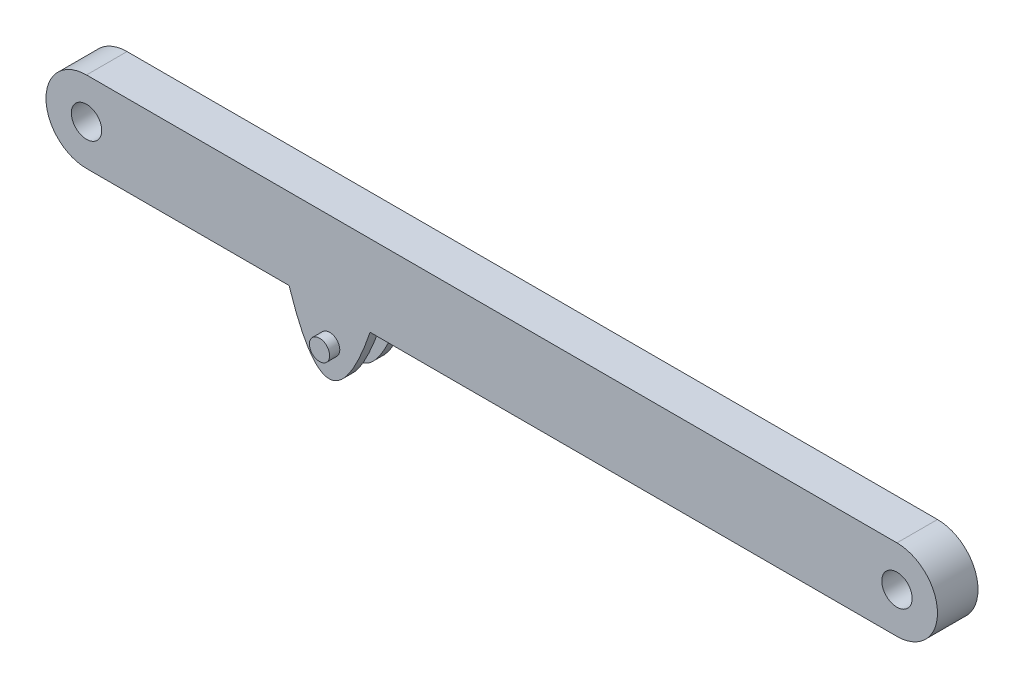
SolidWorks part; units mm, degrees
material "AISI 304"
ref_plane "Front Plane" through (0, 0, 0) normal (0, 0, 1) x (1, 0, 0)
ref_plane "Top Plane" through (0, 0, 0) normal (0, 1, 0) x (1, 0, 0)
ref_plane "Right Plane" through (0, 0, 0) normal (1, 0, 0) x (0, 0, -1)
sketch "Sketch2" plane through (0, 0, 0) normal (0, 0, 1) x (1, 0, 0)
  line L0 (-200, 0) -> (200, 0) construction
  line L1 (-200, 20) -> (200, 20)
  line L2 (-200, -20) -> (200, -20)
  arc A0 (-200, 20) -> (-200, -20) centre (-200, 0) ccw
  arc A1 (200, -20) -> (200, 20) centre (200, 0) ccw
  point P2 (0, 0)
extrude "Boss-Extrude1" add sketch "Sketch2" along normal blind 20
sketch "Sketch4" plane through (0, 0, 20) normal (0, 0, 1) x (1, 0, 0)
  circle A0 centre (-200, 0) radius 7.5
  circle A1 centre (200, 0) radius 7.5
extrude "Cut-Extrude1" cut sketch "Sketch4" against normal blind 20 contours A1 | A0
ref_plane "Plane1" through (0, 0, 10) normal (0, 0, 1) x (1, 0, 0)
sketch "Sketch8" plane through (0, 0, 0) normal (0, 0, 1) x (1, 0, 0)
  line L0 (-100.0376, -20) -> (-60.0376, -20)
  line L1 (-200, -20) -> (200, -20) construction
  spline S0 degree 2 poles (-100.0376, -20) (-80.4932, -80.0015) (-60.0376, -20) knots 0 0 0 1 1 1
extrude "Boss-Extrude2" add sketch "Sketch8" along normal blind 5
sketch "Sketch9" plane through (0, 0, 0) normal (0, 0, 1) x (1, 0, 0)
  circle A0 centre (-80, -35) radius 5
extrude "Boss-Extrude3" add sketch "Sketch9" along normal blind 10 and the other way blind 5
mirror "Mirror2" about plane through (0, 0, 10) normal (0, 0, 1) of "Boss-Extrude3", "Boss-Extrude2"
